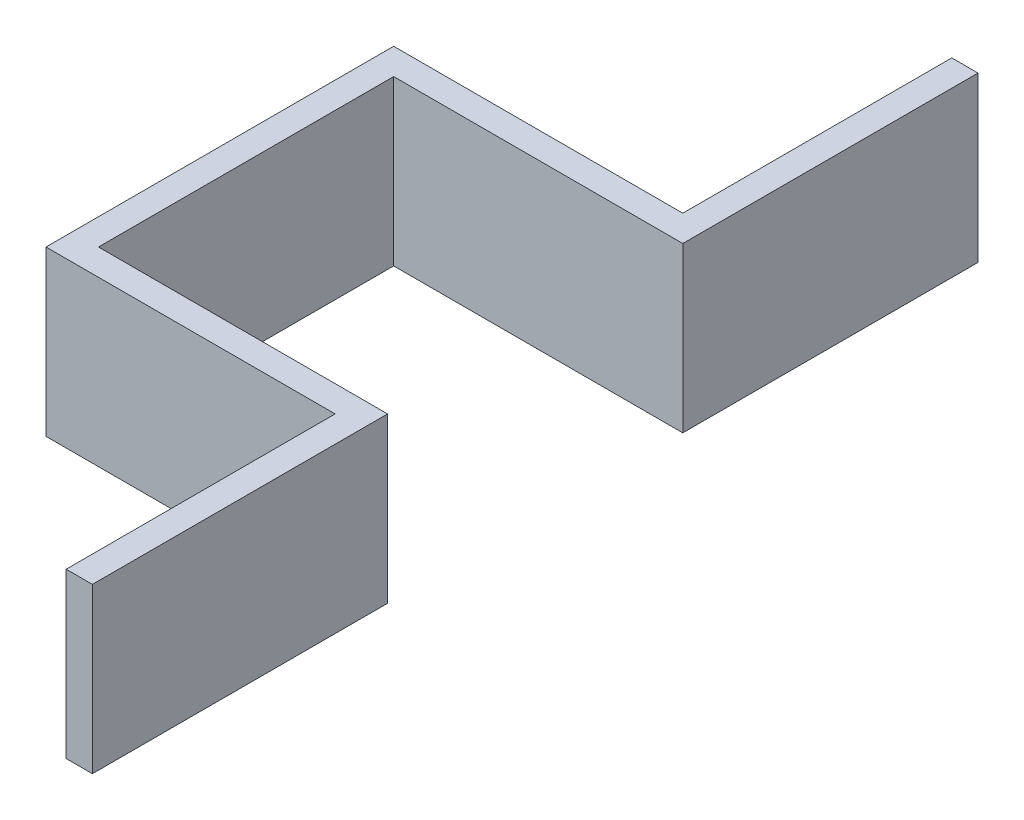
SolidWorks part; units mm, degrees
ref_plane "Front Plane" through (0, 0, 0) normal (0, 0, 1) x (1, 0, 0)
ref_plane "Top Plane" through (0, 0, 0) normal (0, 1, 0) x (1, 0, 0)
ref_plane "Right Plane" through (0, 0, 0) normal (1, 0, 0) x (0, 0, -1)
ref_plane "Plane1" through (0, 5, 0) normal (0, 1, 0) x (1, 0, 0)
sketch "Sketch1" plane through (0, 5, 0) normal (0, 1, 0) x (1, 0, 0)
  line B0 (-194.1023, 167.5) -> (-190.1023, 167.5)
  line B1 (-190.1023, 167.5) -> (-190.1023, 212.5)
  line B2 (-190.1023, 212.5) -> (-234.1745, 212.5)
  line B3 (-234.1745, 212.5) -> (-234.1745, 257.5)
  line B4 (-234.1745, 257.5) -> (-190.1023, 257.5)
  line B5 (-190.1023, 257.5) -> (-190.1023, 302.5)
  line B6 (-190.1023, 302.5) -> (-194.1023, 302.5)
  line B7 (-194.1023, 302.5) -> (-194.1023, 261.5)
  line B8 (-194.1023, 261.5) -> (-238.1745, 261.5)
  line B9 (-238.1745, 261.5) -> (-238.1745, 208.5)
  line B10 (-238.1745, 208.5) -> (-194.1023, 208.5)
  line B11 (-194.1023, 208.5) -> (-194.1023, 167.5)
sketch_block_instance "Block1-1"
sketch_block "Block1"
extrude "Boss-Extrude1" add sketch "Sketch1" against normal blind 25
